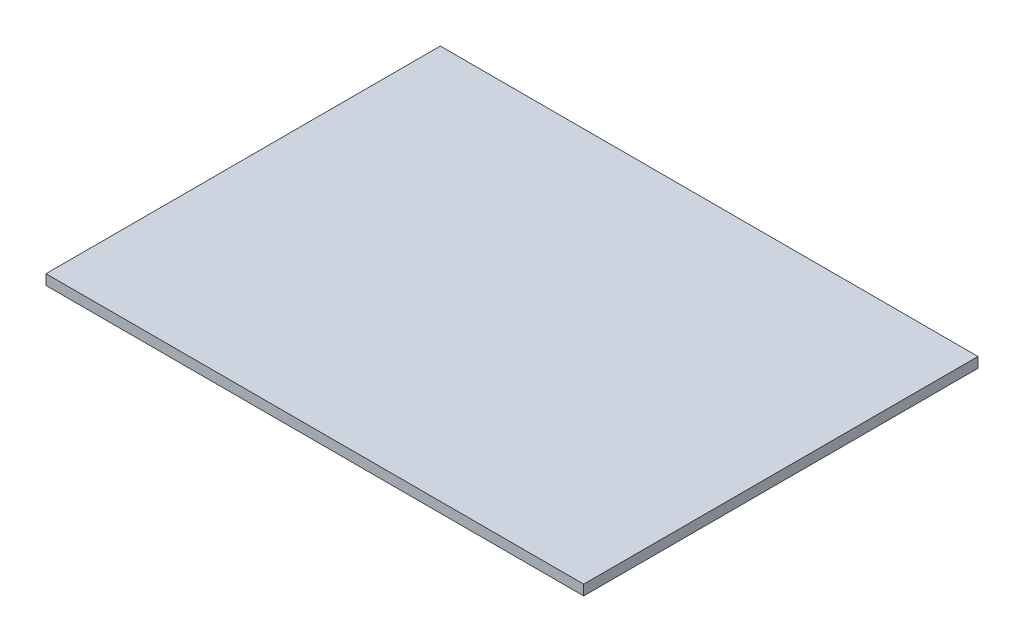
SolidWorks part; units mm, degrees
ref_plane "Front Plane" through (0, 0, 0) normal (0, 0, 1) x (1, 0, 0)
ref_plane "Top Plane" through (0, 0, 0) normal (0, 1, 0) x (1, 0, 0)
ref_plane "Right Plane" through (0, 0, 0) normal (1, 0, 0) x (0, 0, -1)
sketch "Sketch2" plane through (0, 0, 0) normal (0, 1, 0) x (1, 0, 0)
  line L1 (-52.5, -38.5) -> (52.5, -38.5)
  line L2 (-52.5, -38.5) -> (-52.5, 38.5)
  line L3 (-52.5, 38.5) -> (52.5, 38.5)
  line L4 (52.5, -38.5) -> (52.5, 38.5)
  line L5 (-52.5, -38.5) -> (52.5, 38.5) construction
  line L6 (-52.5, 38.5) -> (52.5, -38.5) construction
  point P0 (0, 0)
  dimension "D1" = 105
  dimension "D2" = 77
extrude "Boss-Extrude1" add sketch "Sketch2" along normal blind 2
